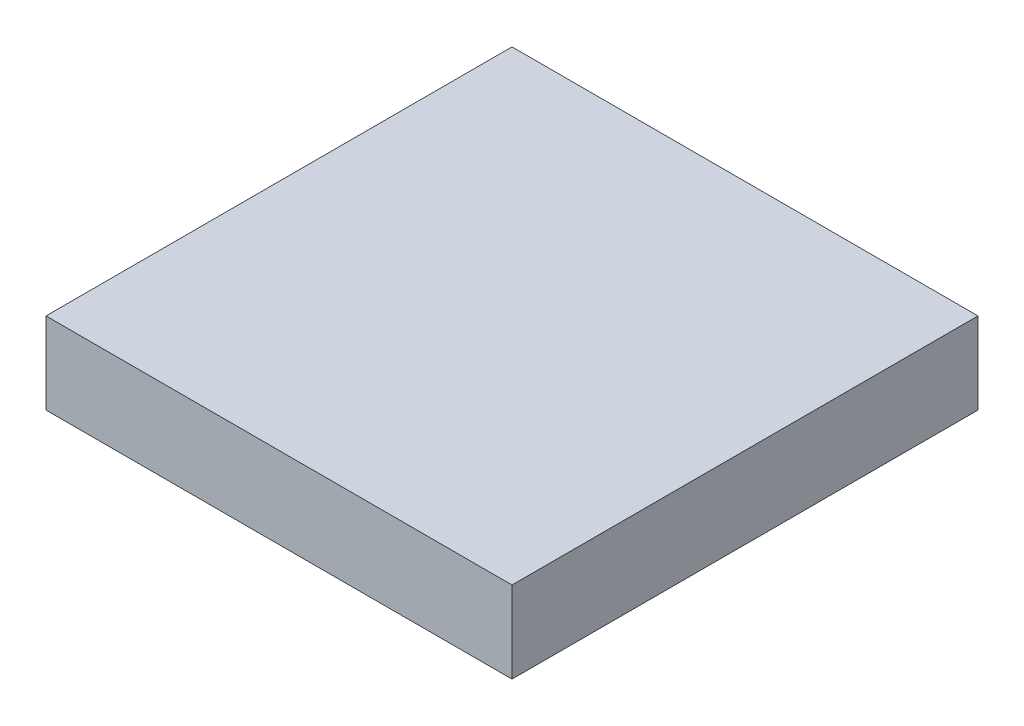
SolidWorks part; units mm, degrees
ref_plane "Front Plane" through (0, 0, 0) normal (0, 0, 1) x (1, 0, 0)
ref_plane "Top Plane" through (0, 0, 0) normal (0, 1, 0) x (1, 0, 0)
ref_plane "Right Plane" through (0, 0, 0) normal (1, 0, 0) x (0, 0, -1)
sketch "Sketch1" plane through (0, 0, 0) normal (0, 1, 0) x (1, 0, 0)
  line L1 (-28.575, -28.575) -> (28.575, -28.575)
  line L2 (-28.575, -28.575) -> (-28.575, 28.575)
  line L3 (-28.575, 28.575) -> (28.575, 28.575)
  line L4 (28.575, -28.575) -> (28.575, 28.575)
  line L5 (-28.575, -28.575) -> (28.575, 28.575) construction
  line L6 (-28.575, 28.575) -> (28.575, -28.575) construction
  point P0 (0, 0)
  dimension "D1" = 57.15
  dimension "D2" = 57.15
extrude "Boss-Extrude1" add sketch "Sketch1" along normal blind 10
sketch "Sketch2" plane through (0, 0, 0) normal (0, 1, 0) x (1, 0, 0)
  line L1 (-28.575, 28.575) -> (28.575, 28.575)
  line L2 (-28.575, 28.575) -> (-28.575, -28.575)
  line L3 (-28.575, -28.575) -> (28.575, -28.575)
  line L4 (28.575, 28.575) -> (28.575, -28.575)
  line L5 (-28.575, 28.575) -> (28.575, -28.575) construction
  line L6 (-28.575, -28.575) -> (28.575, 28.575) construction
  point P0 (0, 0)
  dimension "D1" = 57.15
  dimension "D2" = 57.15
extrude "Boss-Extrude2" add sketch "Sketch2" along normal blind 10 separate body
